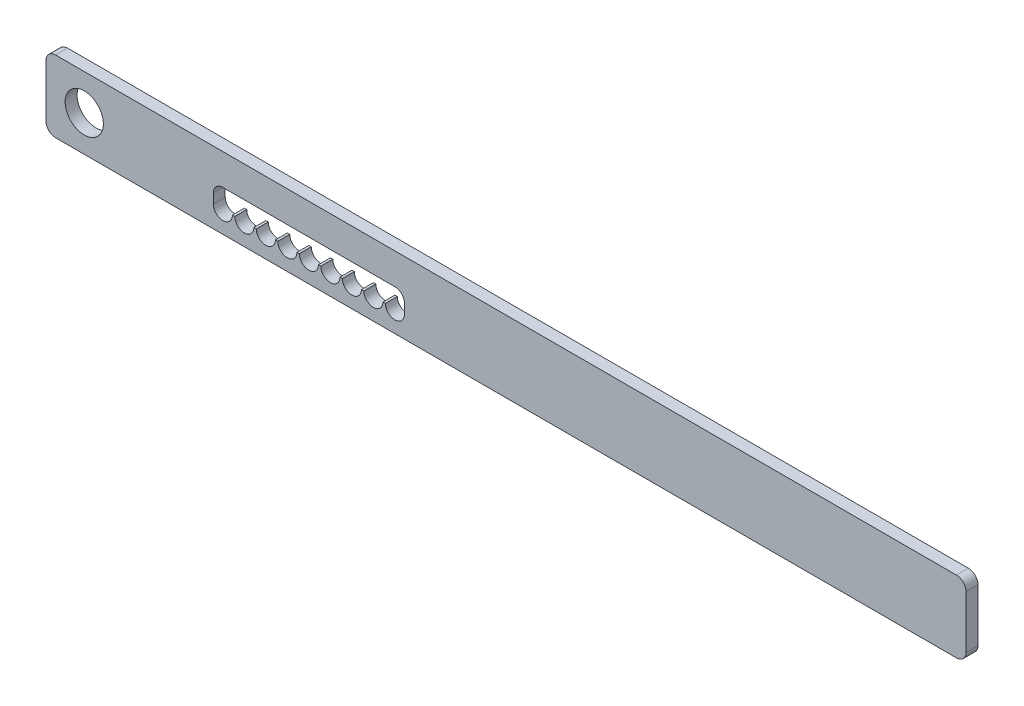
SolidWorks part; units mm, degrees
ref_plane "Plan de face" through (0, 0, 0) normal (0, 0, 1) x (1, 0, 0)
ref_plane "Plan de dessus" through (0, 0, 0) normal (0, 1, 0) x (1, 0, 0)
ref_plane "Plan de droite" through (0, 0, 0) normal (1, 0, 0) x (0, 0, -1)
sketch "Esquisse1" plane through (0, 0, 0) normal (0, 0, 1) x (1, 0, 0)
  line L0 (-192.5, 0) -> (192.5, 0)
other "Elément mécano-soudé1"
ref_plane "Plan1" through (-192.5, 0, 0) normal (1, 0, 0) x (0, 1, 0)
sketch "plat" plane through (-192.5, 0, 0) normal (1, 0, 0) x (0, 1, 0)
  line L0 (-15, 0) -> (15, 0) construction
  line L1 (-15, 2.5) -> (15, 2.5)
  line L2 (-15, 2.5) -> (-15, -2.5)
  line L3 (-15, -2.5) -> (15, -2.5)
  line L4 (15, 2.5) -> (15, -2.5)
  line L5 (0, 2.5) -> (0, -2.5) construction
  point P8 (0, 0)
  dimension "B" = 30
  dimension "A" = 5
sketch "Esquisse2" plane through (0, 0, 2.5) normal (0, 0, 1) x (1, 0, 0)
  line L0 (-192.5, 15) -> (-192.5, -15) construction
  circle A0 centre (-176.5, 0) radius 8
  dimension "D1" = 16
  dimension "D2" = 16
extrude "Enlèv. mat.-Extru.1" cut sketch "Esquisse2" against normal blind 10
sketch "Esquisse3" plane through (0, 0, 2.5) normal (0, 0, 1) x (1, 0, 0)
  line L0 (-192.5, 0) -> (192.5, 0) construction
  line L1 (-122.5, 2) -> (-42.5, 2)
  line L2 (-122.5, 2) -> (-122.5, -6)
  line L3 (-122.5, -6) -> (-42.5, -6)
  line L4 (-42.5, 2) -> (-42.5, -6)
  line L5 (-122.5, 2) -> (-42.5, -6) construction
  line L6 (-122.5, -6) -> (-42.5, 2) construction
  line L8 (-192.5, 15) -> (-192.5, -15) construction
  point P0 (-82.5, -2)
  dimension "D1" = 8
  dimension "D2" = 2
  dimension "D3" = 80
  dimension "D4" = 70
extrude "Enlèv. mat.-Extru.2" cut sketch "Esquisse3" against normal blind 10
fillet "Congé1" radius 4 2 edges at (-42.5, 2, 0) (-122.5, 2, 0)
sketch "Esquisse4" plane through (0, 0, 2.5) normal (0, 0, 1) x (1, 0, 0)
  line L0 (-122.5, -6) -> (-42.5, -6) construction
  line L1 (-122.5, -2) -> (-122.5, -6) construction
  circle A0 centre (-118.5, -6) radius 4
  dimension "D1" = 8
  dimension "D2" = 4
extrude "Enlèv. mat.-Extru.3" cut sketch "Esquisse4" against normal blind 10
pattern_linear "Répétition linéaire1" count 9 spacing 9 along (1, 0, 0) of "Enlèv. mat.-Extru.3"
fillet "Congé2" radius 4 4 edges at (192.5, -15, 0) (192.5, 15, 0) (-192.5, -15, 0) (-192.5, 15, 0)
